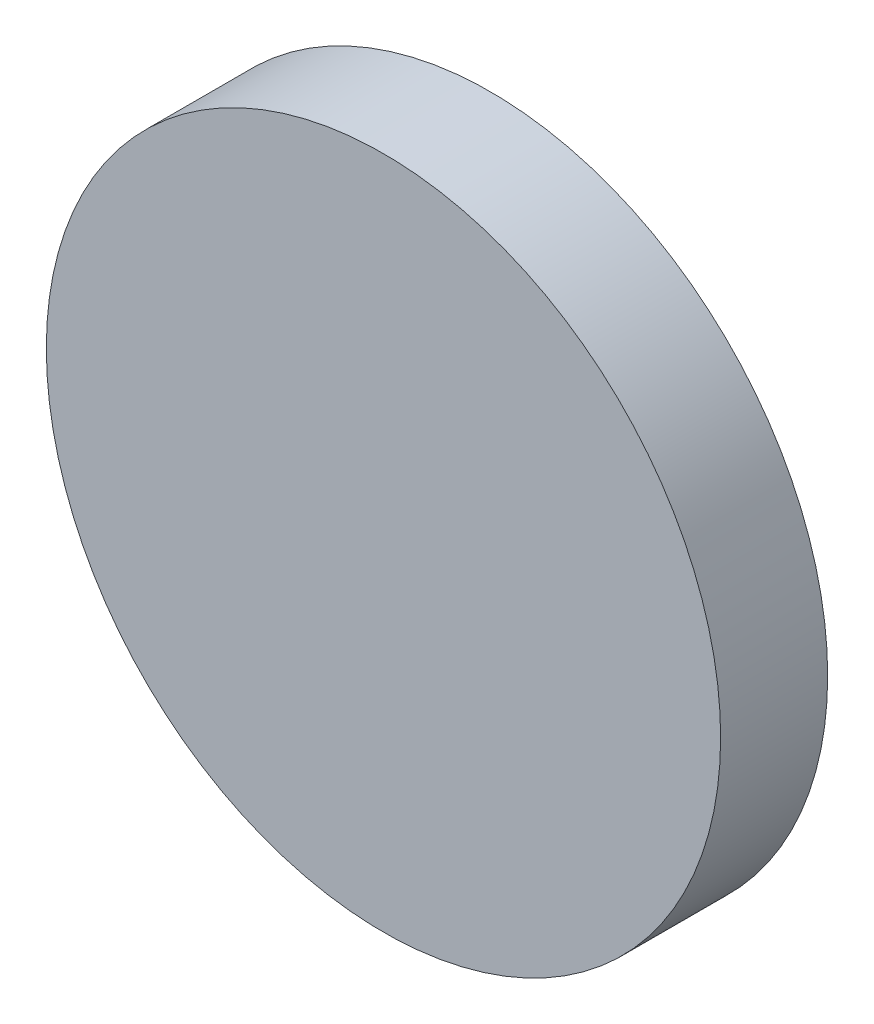
SolidWorks part; units mm, degrees
ref_plane "前视基准面" through (0, 0, 0) normal (0, 0, 1) x (1, 0, 0)
ref_plane "上视基准面" through (0, 0, 0) normal (0, 1, 0) x (1, 0, 0)
ref_plane "右视基准面" through (0, 0, 0) normal (1, 0, 0) x (0, 0, -1)
sketch "草图1" plane through (0, 0, 0) normal (0, 0, 1) x (1, 0, 0)
  circle A0 centre (0, 0) radius 3.15
  dimension "D1" = 6.3
extrude "凸台-拉伸1" add sketch "草图1" along normal blind 1 contours A0
